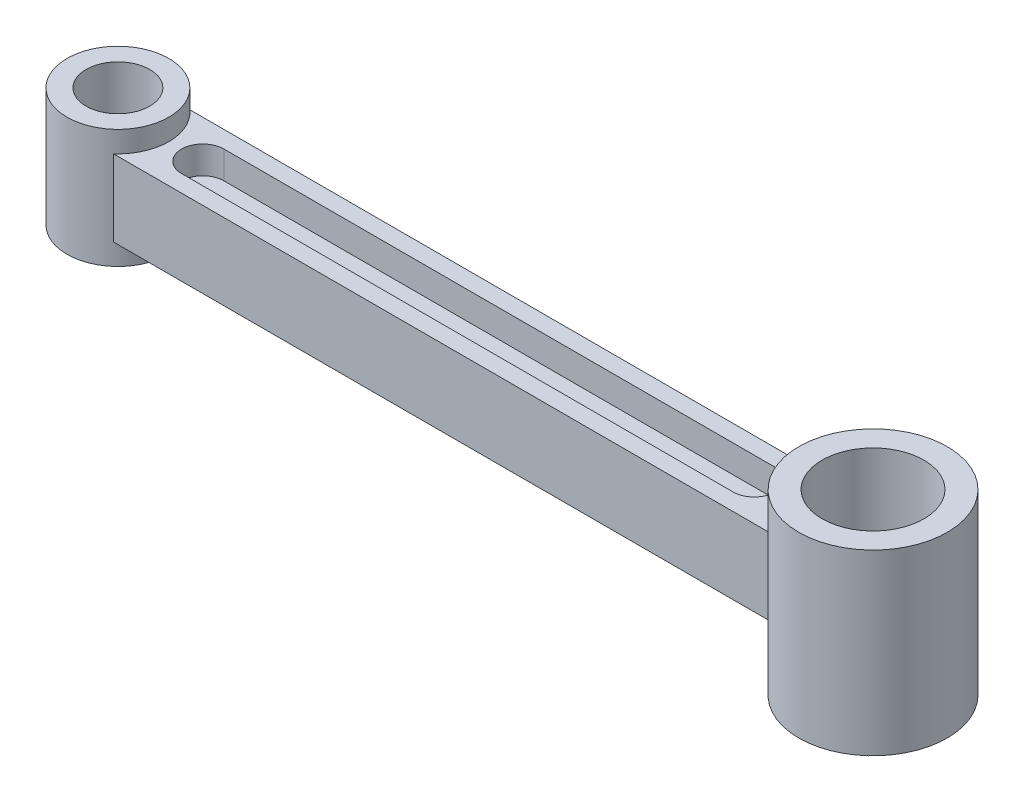
SolidWorks part; units mm, degrees
ref_plane "Front Plane" through (0, 0, 0) normal (0, 0, 1) x (1, 0, 0)
ref_plane "Top Plane" through (0, 0, 0) normal (0, 1, 0) x (1, 0, 0)
ref_plane "Right Plane" through (0, 0, 0) normal (1, 0, 0) x (0, 0, -1)
sketch "Sketch1" plane through (0, 0, 0) normal (0, 1, 0) x (1, 0, 0)
  circle A0 centre (0, 0) radius 7.5
  circle A1 centre (0, 0) radius 12
  dimension "D1" = 24
  dimension "D2" = 15
extrude "Boss-Extrude1" add sketch "Sketch1" along normal mid plane 28
sketch "Sketch6" plane through (0, 0, 0) normal (0, 1, 0) x (1, 0, 0)
  circle A0 centre (178, 0) radius 12
  circle A1 centre (178, 0) radius 17.5
  dimension "D1" = 24
  dimension "D2" = 35
extrude "Boss-Extrude4" add sketch "Sketch6" along normal mid plane 42 separate body
sketch "Sketch14" plane through (0, 0, 0) normal (0, 1, 0) x (1, 0, 0)
  line L1 (7.9373, -9) -> (162.9917, -9)
  line L3 (7.9373, 9) -> (162.9917, 9)
  circle A0 centre (0, 0) radius 12 construction
  arc A1 (7.9373, -9) -> (7.9373, 9) centre (0, 0) ccw
  circle A2 centre (178, 0) radius 17.5 construction
  arc A3 (162.9917, 9) -> (162.9917, -9) centre (178, 0) ccw
  dimension "D1" = 18
  dimension "D2" = 9
extrude "Boss-Extrude5" add sketch "Sketch14" along normal mid plane 18
sketch "Sketch16" plane through (0, 9, 0) normal (0, 1, 0) x (1, 0, 0)
  line L1 (20, 5) -> (150, 5)
  line L3 (20, -5) -> (150, -5)
  arc A0 (20, 5) -> (20, -5) centre (20, 0) ccw
  arc A1 (150, -5) -> (150, 5) centre (150, 0) ccw
  dimension "D4" = 10
  dimension "D5" = 10
  dimension "D1" = 130
  dimension "D2" = 10
  dimension "D3" = 5
  dimension "D6" = 20
extrude "Cut-Extrude4" cut sketch "Sketch16" against normal blind 6.5 contours L1 A1 L3 A0
mirror "Mirror1" about plane through (0, 0, 0) normal (0, 1, 0) of "Cut-Extrude4"
